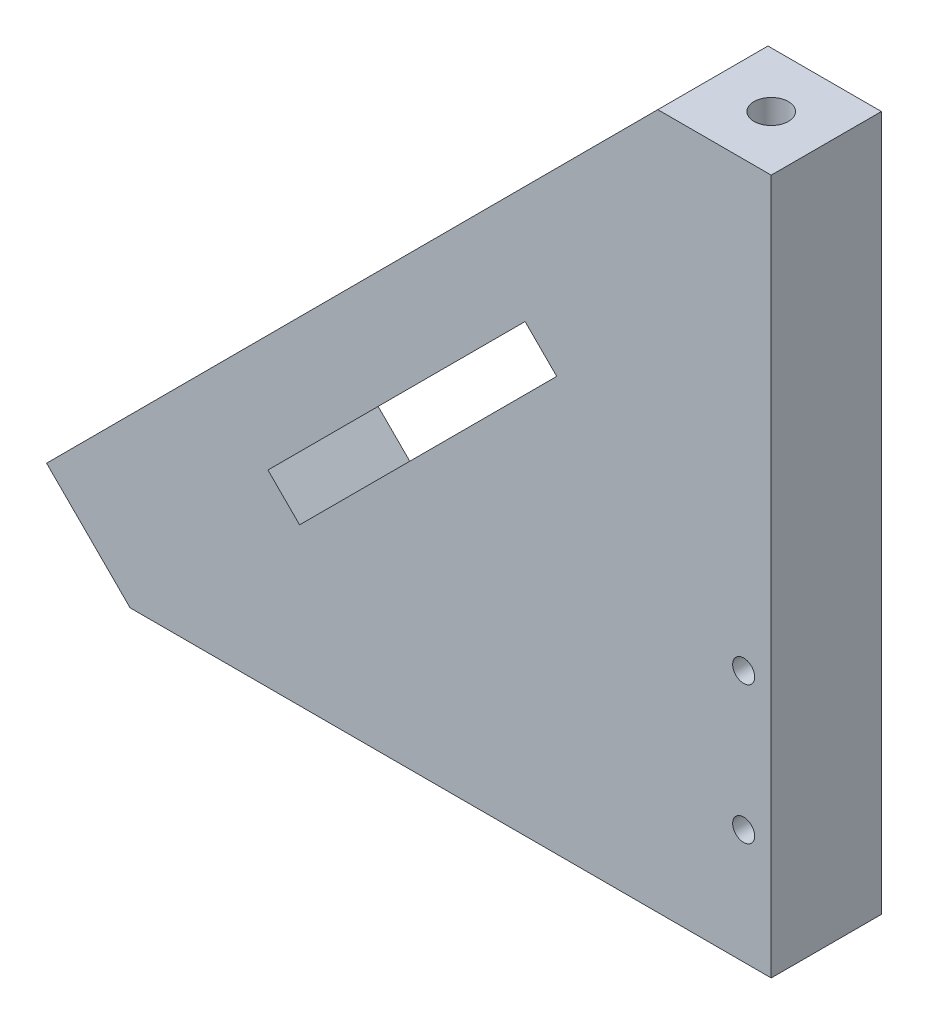
SolidWorks part; units mm, degrees
material "A286 Iron Base Superalloy"
ref_plane "Front Plane" through (0, 0, 0) normal (0, 0, 1) x (1, 0, 0)
ref_plane "Top Plane" through (0, 0, 0) normal (0, 1, 0) x (1, 0, 0)
ref_plane "Right Plane" through (0, 0, 0) normal (1, 0, 0) x (0, 0, -1)
sketch "Sketch2" plane through (0, 0, 0) normal (0, 0, 1) x (1, 0, 0)
  line L0 (-8.3606, 17.4092) -> (51.3194, 17.4092)
  line L1 (51.3194, 17.4092) -> (51.3194, 71.6536)
  line L2 (51.3194, 71.6536) -> (36.0094, 71.6536)
  line L3 (36.0094, 71.6536) -> (43.084, 64.586)
  line L4 (43.084, 64.586) -> (-1.286, 20.1717)
  line L5 (-1.286, 20.1717) -> (-8.3606, 27.2392)
  line L6 (-8.3606, 27.2392) -> (-8.3606, 17.4092)
  dimension "D1" = 10
  dimension "D2" = 10
  dimension "D3" = 15.31
  dimension "D4" = 9.83
  dimension "D5" = 59.68
  dimension "D6" = 62.78
  dimension "D7" = 54.2443
extrude "Boss-Extrude1" add sketch "Sketch2" along normal mid plane 8
sketch "Sketch3" plane through (0, 17.4092, 0) normal (0, -1, 0) x (1, 0, 0)
  line L1 (-8.3606, -4) -> (51.3194, -4)
  line L2 (-8.3606, -4) -> (-8.3606, 4)
  line L3 (-8.3606, 4) -> (51.3194, 4)
  line L4 (51.3194, -4) -> (51.3194, 4)
extrude "Boss-Extrude2" add sketch "Sketch3" along normal blind 5.46
sketch "Sketch4" plane through (0, 0, -4) normal (0, 0, -1) x (-1, 0, 0)
  line L0 (-33.4508, 46.4453) -> (-35.7489, 44.1472)
  line L1 (-35.7489, 44.1472) -> (-17.0812, 25.4796)
  line L2 (-17.0812, 25.4796) -> (-14.7831, 27.7777)
  line L3 (-14.7831, 27.7777) -> (-33.4508, 46.4453)
  dimension "D1" = 30.46
  dimension "D2" = 3.25
  dimension "D4" = 26.4
extrude "Cut-Extrude1" cut sketch "Sketch4" against normal through all
sketch "Sketch5" plane through (0, 0, -4) normal (0, 0, -1) x (-1, 0, 0)
  line L0 (8.3606, 27.2392) -> (8.3606, 11.9492) construction
  line L1 (-51.3194, 11.9492) -> (8.3606, 11.9492)
  line L2 (-51.3194, 11.9492) -> (-51.3194, 14.1092)
  line L3 (-51.3194, 14.1092) -> (8.3606, 14.1092)
  line L4 (8.3606, 11.9492) -> (8.3606, 14.1092)
  dimension "D1" = 2.16
extrude "Cut-Extrude2" cut sketch "Sketch5" against normal blind 10
sketch "Sketch7" plane through (0, 0, -4) normal (0, 0, -1) x (-1, 0, 0)
  line L0 (1.286, 20.1717) -> (-5.0823, 13.8035)
  line L2 (8.3606, 14.1092) -> (8.3606, 29.0434)
  line L3 (8.3606, 29.0434) -> (1.286, 29.0434)
  line L4 (1.286, 20.1717) -> (1.286, 29.0434)
  line L5 (-5.0823, 13.8035) -> (8.3606, 13.8035)
  line L6 (8.3606, 13.8035) -> (8.3606, 14.1092)
extrude "Cut-Extrude7" cut sketch "Sketch7" against normal blind 10
sketch "Sketch8" plane through (-10.7295, 10.7188, 0) normal (-0.7075, 0.7068, 0) x (0, 0, 1)
  line L0 (4, 13.3575) -> (-4, 13.3575) construction
  line L1 (4, 76.1418) -> (-4, 76.1418) construction
  circle A0 centre (0, 71.1418) radius 1.5
  circle A1 centre (0, 18.3575) radius 1.5
  point P4 (0, 13.3575)
  dimension "D1" = 3
  dimension "D2" = 3
  dimension "D3" = 5
  dimension "D4" = 5
sketch "Sketch9" plane through (51.3194, 0, 0) normal (1, 0, 0) x (0, 0, -1)
  line L1 (-4, 71.6536) -> (4, 71.6536) construction
  circle A0 centre (0, 52.6536) radius 1.5
  dimension "D1" = 3
  dimension "D2" = 19
hole_wizard "CBORE for M3 SHCS1" positions "Sketch11" profile "Sketch10" counterbore size "M3" standard "ANSI Metric"
sketch "Sketch11" plane through (51.3194, 0, 0) normal (1, 0, 0) x (0, 0, -1)
  point P0 (0, 52.6536)
sketch "Sketch10" plane through (51.3194, 52.6536, 0) normal (0, 1, 0) x (0, 0, -1)
  line L0 (0, 0) -> (0, 52.6054)
  line L1 (0, 52.6054) -> (1.7, 52.6054)
  line L3 (1.7, 52.6054) -> (1.7, 3)
  line L4 (1.7, 3) -> (3.25, 3)
  line L5 (3.25, 3) -> (3.25, 0)
  line L7 (3.25, 0) -> (0, 0)
  line L11 (0, -6.35) -> (0, 107.95) construction
  dimension "Thru Hole Dia." = 3.4
  dimension "Thru Hole Depth" = 52.6054
  dimension "C'Bore Dia." = 6.5
  dimension "C'Bore Depth" = 3
sketch "Sketch13" plane through (0, 0, -4) normal (0, 0, -1) x (-1, 0, 0)
  line L0 (-4.7765, 14.1092) -> (-51.3194, 14.1092) construction
  line L1 (-51.3194, 14.1092) -> (-51.3194, 71.6536) construction
  circle A0 centre (-49.3194, 32.4292) radius 1.5
  circle A1 centre (-49.3194, 22.4292) radius 1.5
  dimension "D1" = 3
  dimension "D2" = 3
  dimension "D3" = 8.32
  dimension "D4" = 10
  dimension "D5" = 2
  dimension "D6" = 2
sketch "Sketch16" plane through (0, 0, 4) normal (0, 0, 1) x (1, 0, 0)
  line L0 (51.3194, 14.1092) -> (4.7765, 14.1092) construction
  line L1 (51.3194, 14.1092) -> (51.3194, 71.6536) construction
  circle A0 centre (49.3194, 32.4292) radius 1.5
  circle A1 centre (49.3194, 22.4292) radius 1.5
  dimension "D1" = 3
  dimension "D2" = 3
  dimension "D3" = 10
  dimension "D4" = 8.32
  dimension "D5" = 2
  dimension "D6" = 2
hole_wizard "M2x0.4 Tapped Hole1" positions "Sketch18" profile "Sketch17" tap size "M2x0.4" standard "ANSI Metric"
sketch "Sketch18" plane through (0, 0, 4) normal (0, 0, 1) x (1, 0, 0)
  point P0 (49.3194, 32.4292)
  point P3 (49.3194, 22.4292)
sketch "Sketch17" plane through (49.3194, 32.4292, 4) normal (1, 0, 0) x (0, -1, 0)
  line L0 (0, 0) -> (0, 7.4807)
  line L1 (0, 7.4807) -> (0.8, 7)
  line L2 (0.8, 7) -> (0.8, 0)
  line L5 (0.8, 0) -> (0, 0)
  line L10 (0, 7.4807) -> (-0.8, 7) construction
  line L11 (0, -6.35) -> (0, 107.95) construction
  dimension "Tap Drill Dia." = 1.6
  dimension "Tap Drill Depth" = 7
  dimension "Drill Angle" = 118
cosmetic thread "Hole Thread3" parameters "D1"=4, "D2"=2
cosmetic thread "Hole Thread4" parameters "D1"=4, "D2"=2
sketch "Sketch19" plane through (0, 14.1092, 0) normal (0, -1, 0) x (1, 0, 0)
  line L0 (4.7765, 4) -> (4.7765, -4) construction
  circle A0 centre (8.7765, 0) radius 1.5
  dimension "D1" = 3
  dimension "D2" = 4
hole_wizard "CBORE for M3 SHCS2" positions "Sketch21" profile "Sketch20" counterbore size "M3" standard "ANSI Metric" end condition through all
sketch "Sketch21" plane through (0, 14.1092, 0) normal (0, -1, 0) x (-1, 0, 0)
  point P0 (-8.7765, 0)
sketch "Sketch20" plane through (8.7765, 14.1092, 0) normal (1, 0, 0) x (0, 0, -1)
  line L0 (0, 0) -> (0, 57.5443)
  line L1 (0, 57.5443) -> (1.7, 57.5443)
  line L3 (1.7, 57.5443) -> (1.7, 3)
  line L4 (1.7, 3) -> (3.25, 3)
  line L5 (3.25, 3) -> (3.25, 0)
  line L7 (3.25, 0) -> (0, 0)
  line L11 (0, -6.35) -> (0, 107.95) construction
  dimension "Thru Hole Dia." = 3.4
  dimension "Thru Hole Depth" = 57.5443
  dimension "C'Bore Dia." = 6.5
  dimension "C'Bore Depth" = 3
sketch "Sketch22" plane through (0, 0, -4) normal (0, 0, -1) x (-1, 0, 0)
  line L0 (-43.084, 64.586) -> (-51.3194, 64.586)
  line L1 (-51.3194, 14.1092) -> (-51.3194, 71.6536) construction
  line L2 (-51.3194, 64.586) -> (-51.3194, 71.6536)
  line L3 (-51.3194, 71.6536) -> (-36.0094, 71.6536)
  line L4 (-36.0094, 71.6536) -> (-43.084, 64.586)
extrude "Cut-Extrude10" cut sketch "Sketch22" against normal through all
sketch "Sketch23" plane through (0, 64.586, 0) normal (0, 1, 0) x (1, 0, 0)
  line L0 (51.3194, -4) -> (51.3194, 4) construction
  line L1 (51.3194, 4) -> (43.084, 4) construction
  circle A0 centre (47.3194, 0) radius 1.5
  dimension "D1" = 3
  dimension "D2" = 4
  dimension "D3" = 4
sketch "Sketch24" plane through (-10.7295, 10.7188, 0) normal (-0.7075, 0.7068, 0) x (0, 0, 1)
  line L0 (4, 76.1418) -> (-4, 76.1418) construction
  line L1 (-4, 76.1418) -> (-4, 13.3618) construction
  circle A0 centre (0, 66.1418) radius 1.5
  dimension "D1" = 3
  dimension "D2" = 10
  dimension "D3" = 4
extrude "Cut-Extrude12" cut sketch "Sketch24" against normal blind 5.5
hole_wizard "M3x0.5 Tapped Hole3" positions "Sketch27" profile "Sketch26" tap size "M3x0.5" standard "ANSI Metric"
sketch "Sketch27" plane through (0, 64.586, 0) normal (0, 1, 0) x (1, 0, 0)
  point P0 (47.3194, 0)
sketch "Sketch26" plane through (47.3194, 64.586, 0) normal (1, 0, 0) x (0, 0, 1)
  line L0 (0, 0) -> (0, 9.2511)
  line L1 (0, 9.2511) -> (1.25, 8.5)
  line L2 (1.25, 8.5) -> (1.25, 0)
  line L5 (1.25, 0) -> (0, 0)
  line L10 (0, 9.2511) -> (-1.25, 8.5) construction
  line L11 (0, -6.35) -> (0, 107.95) construction
  dimension "Tap Drill Dia." = 2.5
  dimension "Tap Drill Depth" = 8.5
  dimension "Drill Angle" = 118
cosmetic thread "Hole Thread5" parameters "D1"=6, "D2"=3
sketch "Sketch28" plane through (0, 0, -4) normal (0, 0, -1) x (-1, 0, 0)
  line L0 (-33.4508, 46.4453) -> (-35.7489, 44.1472) construction
  line L3 (-17.0812, 25.4796) -> (-14.7831, 27.7777) construction
  line L4 (-33.4508, 46.4453) -> (-35.7489, 44.1472)
  line L5 (-29.204, 50.6921) -> (-10.5457, 32.0152)
  line L6 (-43.084, 64.586) -> (1.286, 20.1717) construction
  line L7 (-17.0812, 25.4796) -> (-14.7831, 27.7777)
  line L8 (-35.7489, 44.1472) -> (-40.345, 39.551)
  line L9 (-40.345, 39.551) -> (-21.6774, 20.8834)
  line L10 (-33.4508, 46.4453) -> (-29.204, 50.6921)
  line L12 (-33.4508, 55.6377) -> (-44.9412, 44.1472) construction
  line L13 (-17.0812, 16.2872) -> (-5.5907, 27.7777) construction
  line L14 (-17.0812, 25.4796) -> (-21.6774, 20.8834)
  line L15 (-14.7831, 27.7777) -> (-10.5457, 32.0152)
  line L17 (-44.9412, 44.1472) -> (-17.0812, 16.2872) construction
  line L18 (-5.5907, 27.7777) -> (-33.4508, 55.6377) construction
  line L19 (-35.7489, 44.1472) -> (-17.0812, 25.4796) construction
  line L20 (-14.7831, 27.7777) -> (-33.4508, 46.4453) construction
extrude "Cut-Extrude13" cut sketch "Sketch28" against normal blind 2
